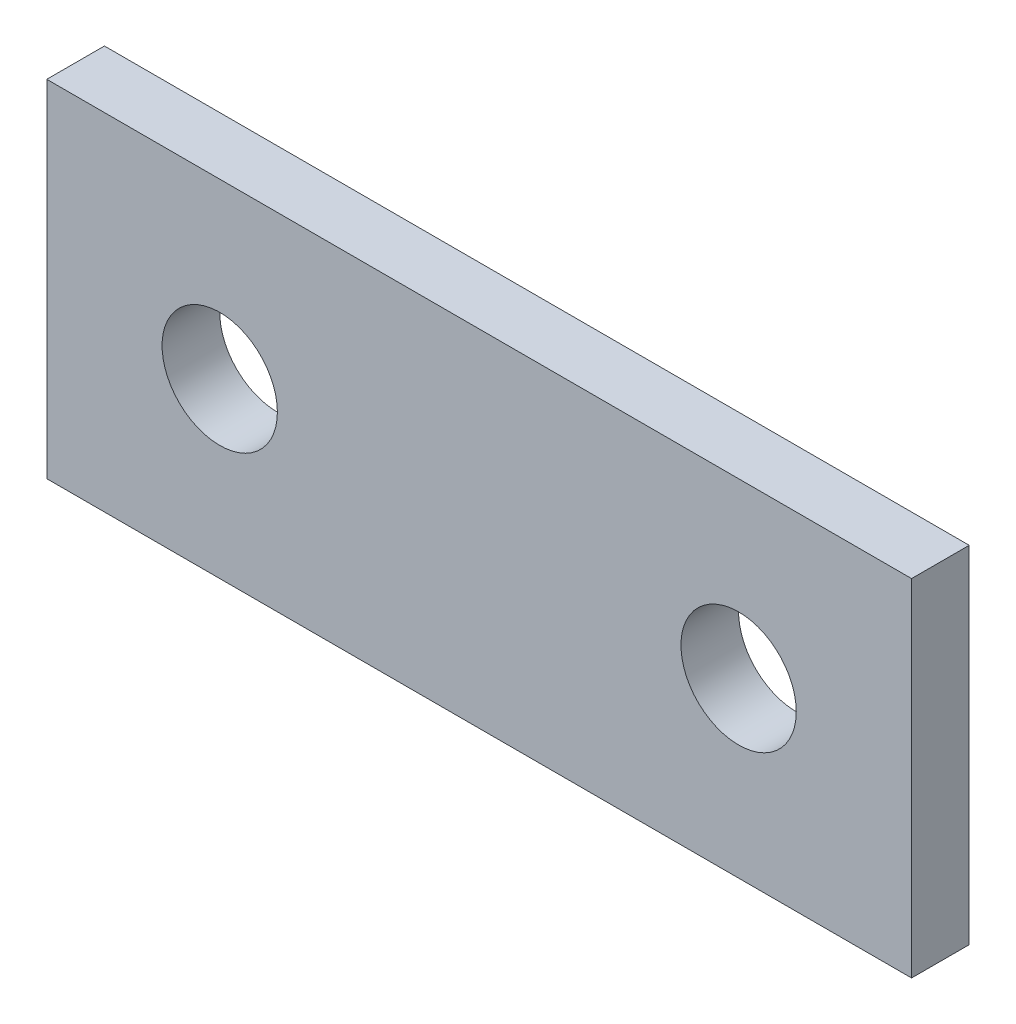
SolidWorks part; units mm, degrees
material "1.4000 (X6Cr13)"
ref_plane "Front Plane" through (0, 0, 0) normal (0, 0, 1) x (1, 0, 0)
ref_plane "Top Plane" through (0, 0, 0) normal (0, 1, 0) x (1, 0, 0)
ref_plane "Right Plane" through (0, 0, 0) normal (1, 0, 0) x (0, 0, -1)
sketch "Sketch1" plane through (0, 0, 0) normal (0, 0, 1) x (1, 0, 0)
  line L0 (-4.5, 0) -> (4.5, 0) construction
  line L1 (-7.5, -3) -> (7.5, -3)
  line L2 (-7.5, -3) -> (-7.5, 3)
  line L3 (-7.5, 3) -> (7.5, 3)
  line L4 (7.5, -3) -> (7.5, 3)
  line L5 (-7.5, -3) -> (7.5, 3) construction
  line L6 (-7.5, 3) -> (7.5, -3) construction
  circle A0 centre (4.5, 0) radius 1
  circle A1 centre (-4.5, 0) radius 1
  point P0 (0, 0)
  point P9 (0, 0)
  dimension "D3" = 2
  dimension "D4" = 2
  dimension "D5" = 3
  dimension "D1" = 15
  dimension "D2" = 6
extrude "Boss-Extrude1" add sketch "Sketch1" along normal blind 1
